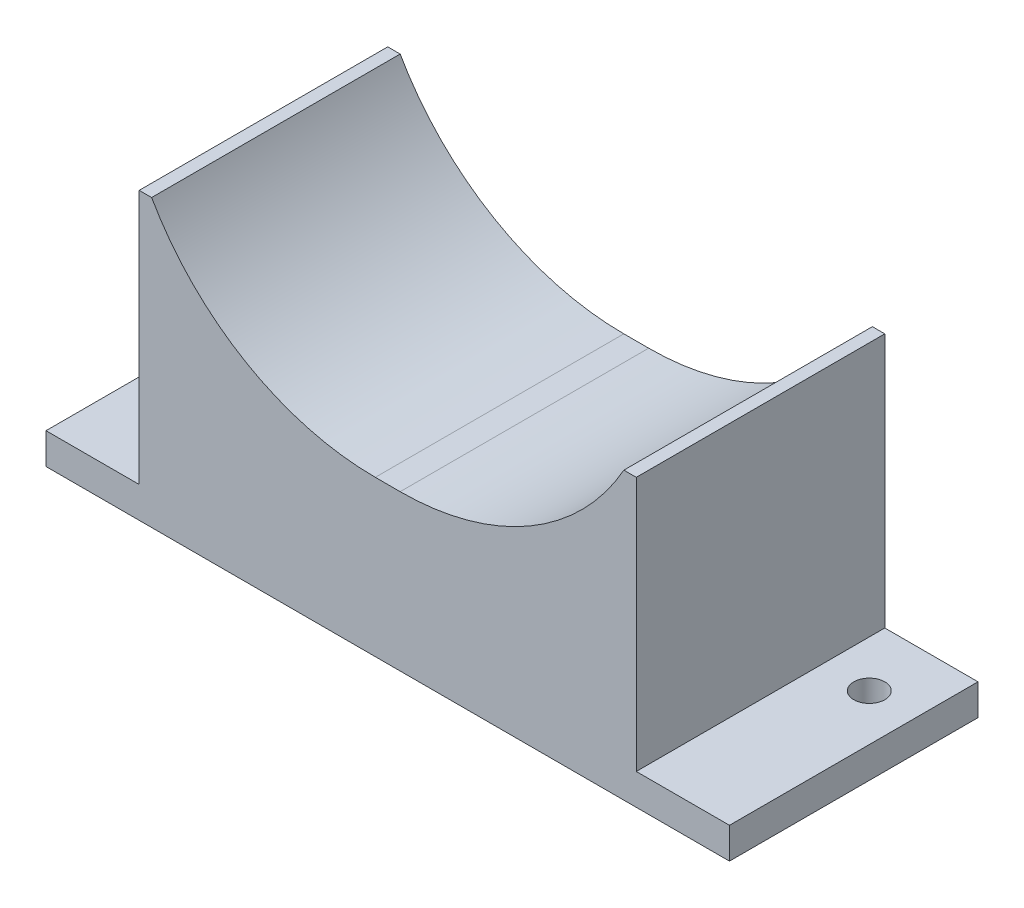
SolidWorks part; units mm, degrees
ref_plane "Front Plane" through (0, 0, 0) normal (0, 0, 1) x (1, 0, 0)
ref_plane "Top Plane" through (0, 0, 0) normal (0, 1, 0) x (1, 0, 0)
ref_plane "Right Plane" through (0, 0, 0) normal (1, 0, 0) x (0, 0, -1)
sketch "Sketch1" plane through (0, 0, 0) normal (0, 0, 1) x (1, 0, 0)
  line L0 (0, 12.6728) -> (0, 0) construction
  line L1 (55, 0) -> (-55, 0)
  line L2 (-55, 0) -> (-55, 5)
  line L3 (-55, 5) -> (-40, 5)
  line L4 (-40, 5) -> (-40, 46)
  line L5 (-40, 46) -> (-38, 46)
  line L6 (2, 25) -> (-2, 25)
  line L7 (40, 46) -> (38, 46)
  line L8 (40, 5) -> (40, 46)
  line L9 (55, 5) -> (40, 5)
  line L10 (55, 0) -> (55, 5)
  arc A0 (-2, 25) -> (-38, 46) centre (-2, 66.3571) cw
  arc A1 (2, 25) -> (38, 46) centre (2, 66.3571) ccw
  point P16 (0, 25)
  dimension "D7" = 2
  dimension "D1" = 38
  dimension "D2" = 21
  dimension "D3" = 25
  dimension "D4" = 15
  dimension "D5" = 2
  dimension "D6" = 5
extrude "Boss-Extrude1" add sketch "Sketch1" along normal blind 40
ref_plane "Plane1" through (55, 5, 0) normal (0, 0, -1) x (-1, 0, 0)
sketch "Sketch3" plane through (0, 5, 0) normal (0, 1, 0) x (1, 0, 0)
  line L0 (-55, -10) -> (55, -10) construction
  line L1 (-55, -40) -> (-55, 0) construction
  line L2 (55, -40) -> (55, 0) construction
  line L3 (0, 0) -> (0, -40) construction
  line L4 (2, 0) -> (-2, 0) construction
  line L5 (2, -40) -> (-2, -40) construction
  line L6 (-40, 0) -> (-55, 0) construction
  circle A0 centre (-47.5, -10) radius 2.5
  circle A1 centre (47.5, -10) radius 2.5
  dimension "D1" = 5
  dimension "D2" = 10
  dimension "D3" = 7.5
extrude "Cut-Extrude1" cut sketch "Sketch3" against normal blind 40
